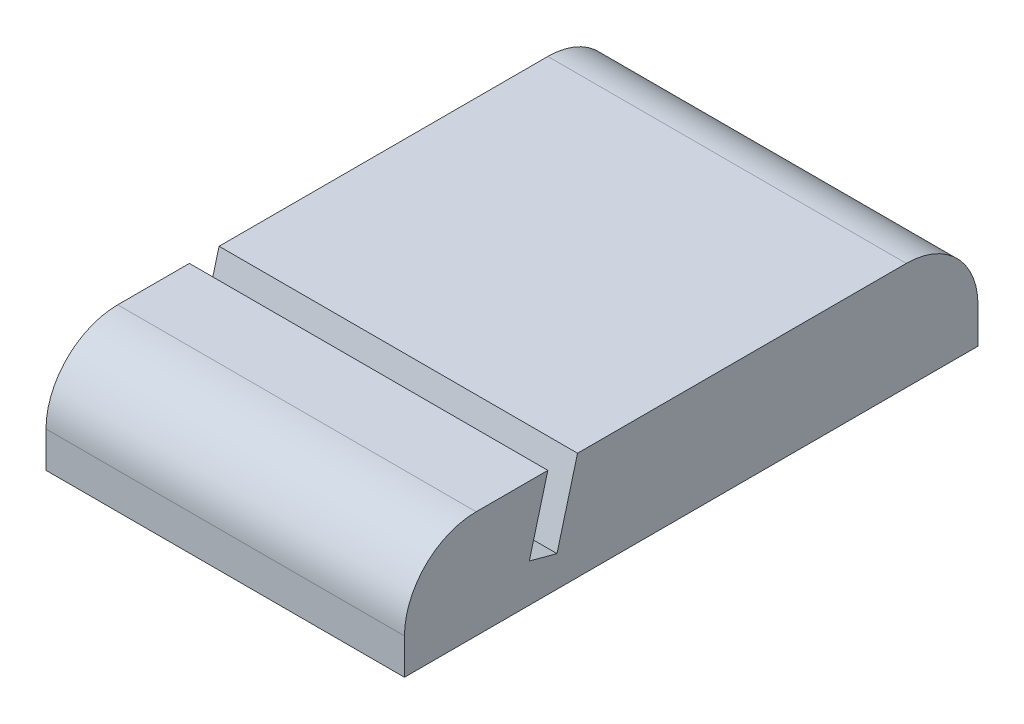
SolidWorks part; units mm, degrees
ref_plane "Plan de face" through (0, 0, 0) normal (0, 0, 1) x (1, 0, 0)
ref_plane "Plan de dessus" through (0, 0, 0) normal (0, 1, 0) x (1, 0, 0)
ref_plane "Plan de droite" through (0, 0, 0) normal (1, 0, 0) x (0, 0, -1)
sketch "Esquisse1" plane through (0, 0, 0) normal (1, 0, 0) x (0, 0, -1)
  line L0 (-40, 0) -> (40, 0)
  line L1 (-40, 0) -> (-40, 15)
  line L2 (-40, 15) -> (-20, 15)
  line L3 (-20, 15) -> (-22.5882, 5.3407)
  line L4 (-22.5882, 5.3407) -> (-18.7245, 4.3055)
  line L5 (-18.7245, 4.3055) -> (-15.8589, 15)
  line L6 (-15.8589, 15) -> (40, 15)
  line L7 (40, 15) -> (40, 0)
  point P3 (0, 0)
  point P4 (0, 0)
  point P7 (0, 0)
  point P12 (4.1862, 7.3475)
  dimension "D1" = 80
  dimension "D2" = 4
  dimension "D3" = 15
  dimension "D4" = 20
  dimension "D5" = 10
  dimension "D6" = 75
extrude "Boss.-Extru.1" add sketch "Esquisse1" along normal blind 50
fillet "Congé1" radius 10 2 edges at (25, 15, -40) (25, 15, 40)
